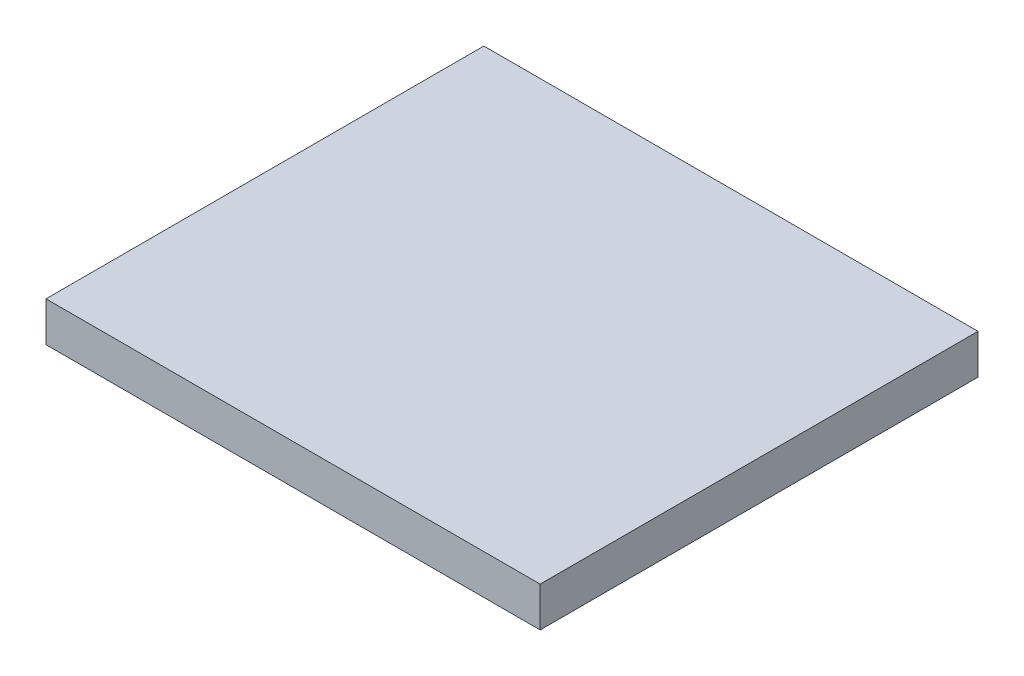
SolidWorks part; units mm, degrees
ref_plane "Front Plane" through (0, 0, 0) normal (0, 0, 1) x (1, 0, 0)
ref_plane "Top Plane" through (0, 0, 0) normal (0, 1, 0) x (1, 0, 0)
ref_plane "Right Plane" through (0, 0, 0) normal (1, 0, 0) x (0, 0, -1)
sketch "Sketch1" plane through (0, 0, 0) normal (0, 1, 0) x (1, 0, 0)
  line L1 (-43.5629, 5.7109) -> (-4.0629, 5.7109)
  line L2 (-43.5629, 5.7109) -> (-43.5629, -29.2891)
  line L3 (-43.5629, -29.2891) -> (-4.0629, -29.2891)
  line L4 (-4.0629, 5.7109) -> (-4.0629, -29.2891)
  dimension "D1" = 35
  dimension "D2" = 39.5
extrude "Boss-Extrude1" add sketch "Sketch1" along normal blind 3.175
